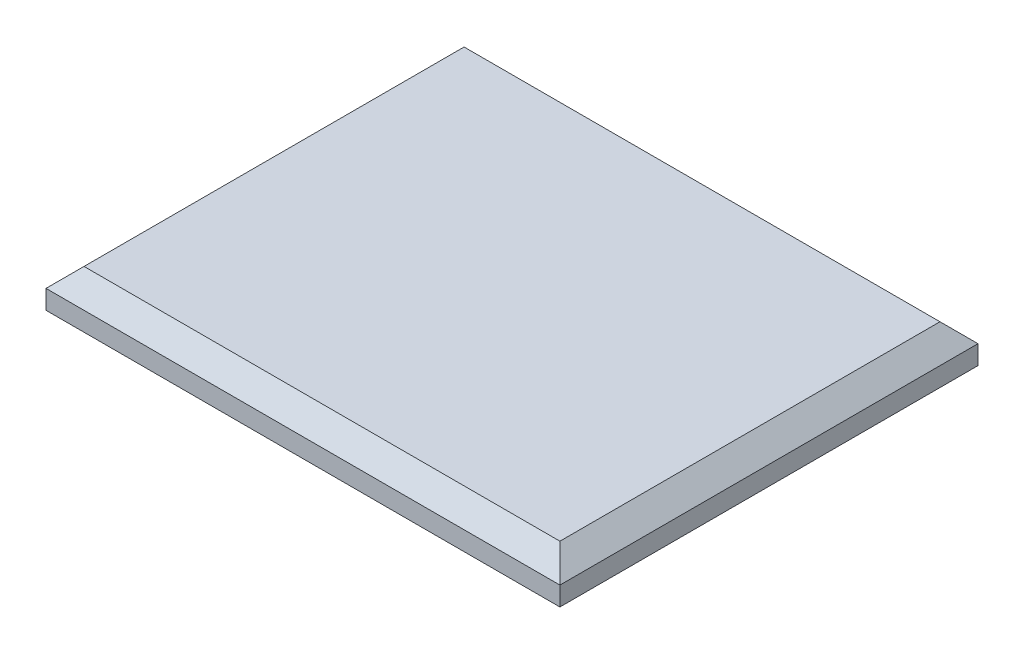
SolidWorks part; units mm, degrees
material "Nickel"
ref_plane "Front Plane" through (0, 0, 0) normal (0, 0, 1) x (1, 0, 0)
ref_plane "Top Plane" through (0, 0, 0) normal (0, 1, 0) x (1, 0, 0)
ref_plane "Right Plane" through (0, 0, 0) normal (1, 0, 0) x (0, 0, -1)
sketch "Sketch1" plane through (0, 0, 0) normal (0, 1, 0) x (1, 0, 0)
  line L1 (-47.605, 40) -> (47.605, 40) construction
  line L2 (-47.605, 40) -> (-47.605, -40) construction
  line L3 (-47.605, -40) -> (47.605, -40) construction
  line L4 (47.605, 40) -> (47.605, -40) construction
  line L5 (-47.605, 40) -> (47.605, -40) construction
  line L6 (-47.605, -40) -> (47.605, 40) construction
  line L7 (-67.605, 55) -> (67.605, 55)
  line L8 (-67.605, 55) -> (-67.605, -55)
  line L9 (-67.605, -55) -> (67.605, -55)
  line L10 (67.605, 55) -> (67.605, -55)
  line L11 (-67.605, 55) -> (67.605, -55) construction
  line L12 (-67.605, -55) -> (67.605, 55) construction
  point P0 (0, 0)
  point P6 (0, 0)
  dimension "D1" = 95.21
  dimension "D2" = 80
  dimension "D3" = 20
  dimension "D4" = 15
extrude "Boss-Extrude1" add sketch "Sketch1" along normal blind 10
chamfer "Chamfer1" distance 5 angle 45 4 edges at (0, 10, -55) (67.605, 10, 0) (0, 10, 55) (-67.605, 10, 0)
